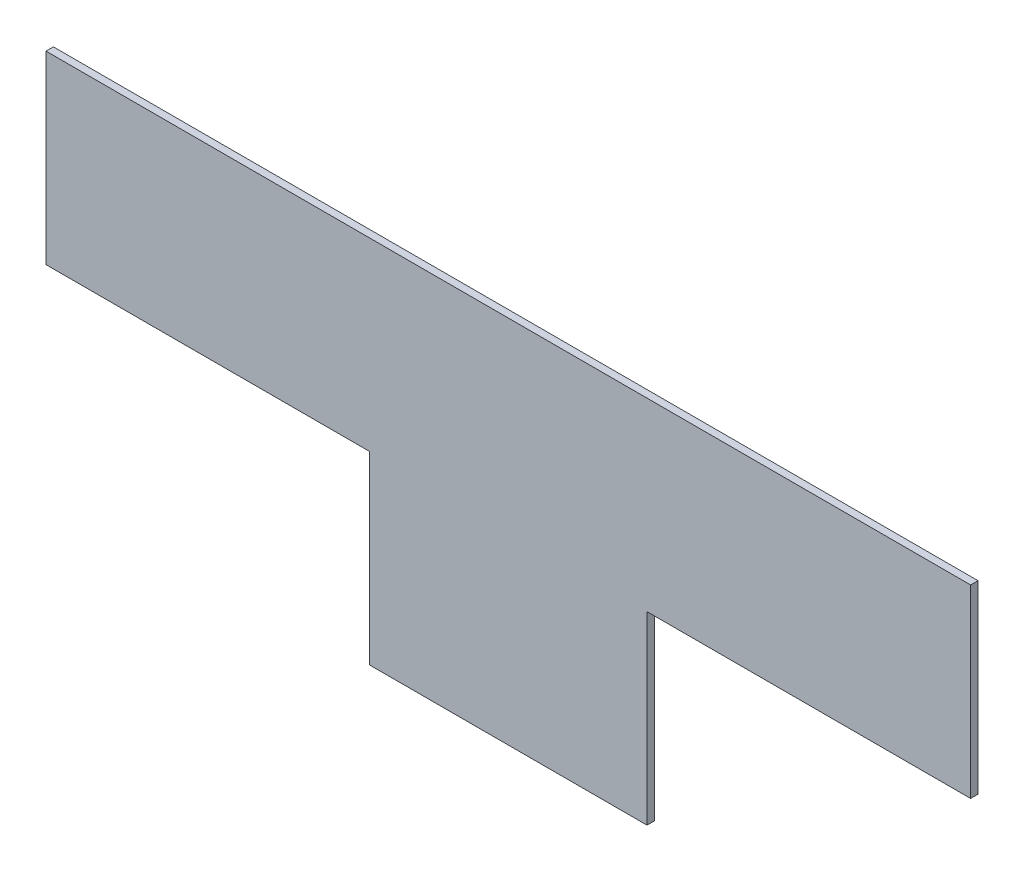
SolidWorks part; units mm, degrees
material "Nylon"
ref_plane "Ebene vorne XY" through (0, 0, 0) normal (0, 0, 1) x (1, 0, 0)
ref_plane "Ebene oben XZ" through (0, 0, 0) normal (0, 1, 0) x (1, 0, 0)
ref_plane "Ebene rechts YZ" through (0, 0, 0) normal (1, 0, 0) x (0, 0, -1)
sketch "Skizze1" plane through (0, 0, 0) normal (0, 0, 1) x (1, 0, 0)
  line L1 (1000, -400) -> (-1000, -400)
  line L2 (1000, -400) -> (1000, 400)
  line L3 (1000, 400) -> (-1000, 400)
  line L4 (-1000, -400) -> (-1000, 400)
  line L5 (1000, -400) -> (-1000, 400) construction
  line L6 (1000, 400) -> (-1000, -400) construction
  point P0 (0, 0)
extrude "Aufsatz-Linear austragen1" add sketch "Skizze1" along normal blind 16
sketch "Skizze2" plane through (0, 0, 16) normal (0, 0, 1) x (1, 0, 0)
  line L0 (-300, -400) -> (-300, 0)
  line L1 (-1000, -400) -> (1000, -400) construction
  line L2 (-300, 0) -> (-1381.9089, 0)
  line L3 (0, 498.0617) -> (0, -498.0617) construction
  line L4 (-1381.9089, 0) -> (-1381.9089, -457.5806)
  line L5 (-1381.9089, -457.5806) -> (-300, -457.5806)
  line L6 (-300, -457.5806) -> (-300, -400)
  line L7 (1381.9089, -457.5806) -> (300, -457.5806)
  line L8 (1381.9089, 0) -> (1381.9089, -457.5806)
  line L9 (300, 0) -> (1381.9089, 0)
  line L10 (300, -400) -> (300, 0)
  line L11 (300, -457.5806) -> (300, -400)
  point P9 (0, 0)
  dimension "D1" = 300
  dimension "D2" = 400
extrude "Schnitt-Linear austragen1" cut sketch "Skizze2" against normal through all
